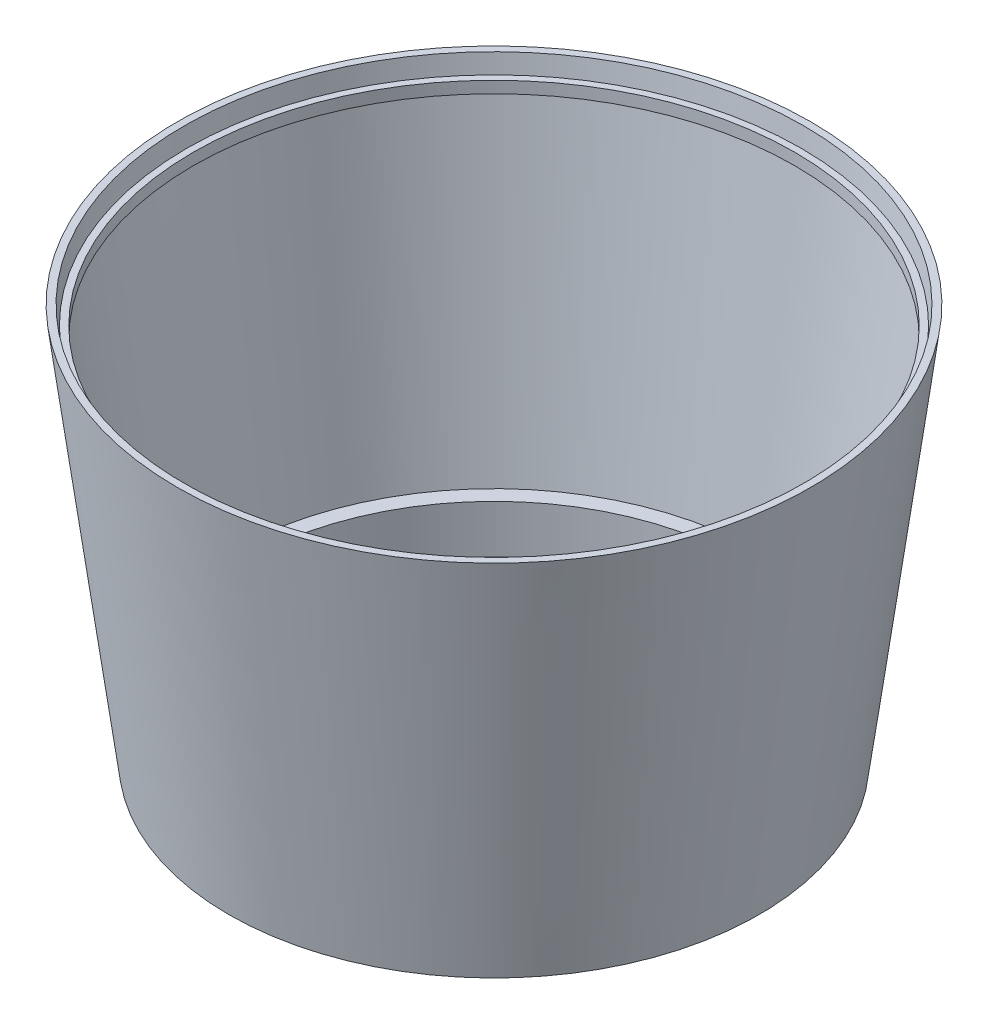
SolidWorks part; units mm, degrees
ref_plane "前视基准面" through (0, 0, 0) normal (0, 0, 1) x (1, 0, 0)
ref_plane "上视基准面" through (0, 0, 0) normal (0, 1, 0) x (1, 0, 0)
ref_plane "右视基准面" through (0, 0, 0) normal (1, 0, 0) x (0, 0, -1)
sketch "草图1" plane through (0, 0, 0) normal (0, 0, 1) x (1, 0, 0)
  line L0 (6.3786, 4.5245) -> (50.5555, 4.5245)
  line L1 (6.3786, 4.5245) -> (6.3786, 149.7613)
  line L2 (50.5555, 4.5245) -> (206.1932, 1201.5139)
  line L3 (206.1932, 1201.5139) -> (184.9678, 1201.5139)
  line L4 (184.9678, 1201.5139) -> (177.7393, 1145.9201)
  line L5 (177.7393, 1145.9201) -> (157.7415, 1145.9201)
  line L6 (157.7415, 1145.9201) -> (157.7415, 1110.5534)
  line L7 (178.3146, 1110.5534) -> (53.3884, 149.7613)
  line L8 (157.7415, 1110.5534) -> (178.3146, 1110.5534)
  line L9 (6.3786, 149.7613) -> (53.3884, 149.7613)
  line L10 (6.3786, 4.5245) -> (-752, 4.5245) construction
  line L11 (-752, 4.5245) -> (-752, 109.4948) construction
  point P2 (206.1932, 1201.5139)
  point P3 (0, 0)
  point P14 (157.7415, 1145.9201)
revolve "旋转1" add sketch "草图1" angle 360 about L11
